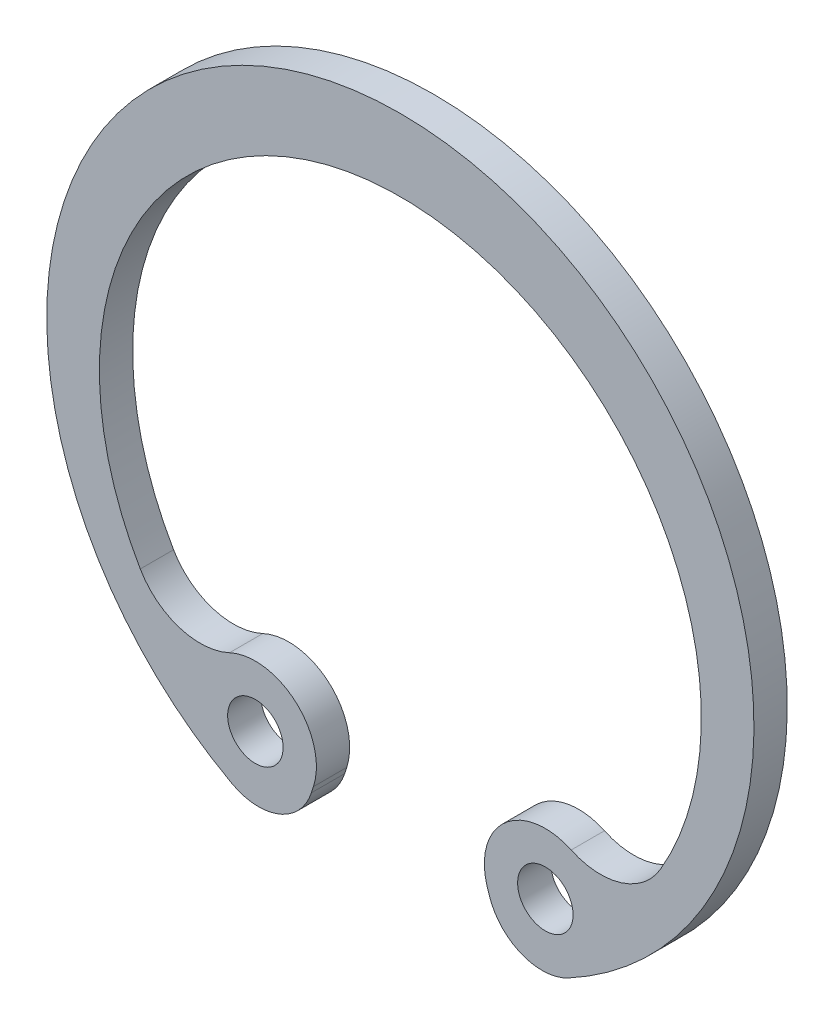
SolidWorks part; units mm, degrees
material "AISI 1020"
ref_plane "Спереди" through (0, 0, 0) normal (0, 0, 1) x (1, 0, 0)
ref_plane "Сверху" through (0, 0, 0) normal (0, 1, 0) x (1, 0, 0)
ref_plane "Справа" through (0, 0, 0) normal (1, 0, 0) x (0, 0, -1)
sketch "Эскиз1" plane through (0, 0, 0) normal (0, 0, 1) x (1, 0, 0)
  line L0 (0, -1000) -> (0, 49000) construction
  line L1 (0, 0) -> (5.7, -9.1144) construction
  line L2 (3.6355, -9.8745) -> (3.7195, -10.1028)
  line L3 (0, 10.35) -> (22.1, 10.35) construction
  arc A0 (6.6186, -11.1309) -> (0, 12.95) centre (0, 0) ccw
  circle A2 centre (5.7, -9.1144) radius 1
  arc A3 (6.5493, -7.085) -> (3.6355, -9.8745) centre (5.7, -9.1144) ccw
  arc A4 (6.5493, -7.085) -> (9.7116, -5.9714) centre (7.5144, -4.7788) ccw
  arc A5 (3.7195, -10.1028) -> (6.6186, -11.1309) centre (5.5964, -9.4119) ccw
  arc A6 (9.7116, -5.9714) -> (0, 10.35) centre (0, -0.7) ccw
  dimension "_d2" = 25.9
  dimension "_d4" = 2
  dimension "_r1" = 2.5
  dimension "_r2" = 2
  dimension "D1" = 11.05
  dimension "_e" = 0.7
  dimension "_a" = 4.4
  dimension "_l" = 7
  dimension "_d3" = 22.1
sketch "Эскиз2" plane through (0, 0, 0) normal (0, 0, 1) x (1, 0, 0)
  line L0 (0, -201000) -> (0, 249000) construction
  line L1 (-3.2086, -10.0704) -> (-3.1339, -9.8388)
  line L2 (3.6355, -9.8745) -> (3.7195, -10.1028) construction
  line L3 (0, 0) -> (6.6186, -11.1309) construction
  line L4 (0, 0) -> (-6.0632, -11.2161) construction
  line L5 (3.7195, -10.1028) -> (6.6186, -11.1309) construction
  line L6 (-6.0632, -11.2161) -> (-3.2086, -10.0704) construction
  line L7 (6.5493, -7.085) -> (3.6355, -9.8745) construction
  line L8 (-6.1593, -7.1707) -> (-3.1339, -9.8388) construction
  line L9 (0, 12.75) -> (0, 13.95) construction
  circle A0 centre (0, 0) radius 12.75 construction
  circle A1 centre (0, 0) radius 12 construction
  circle A2 centre (0, 0) radius 7.1 construction
  arc A3 (0, 12.75) -> (-6.0632, -11.2161) centre (0, 0) ccw
  arc A4 (0, 10.15) -> (-9.3782, -6.1639) centre (0, -0.7025) ccw
  arc A5 (-6.0632, -11.2161) -> (-3.2086, -10.0704) centre (-5.1121, -9.4567) ccw
  arc A6 (-3.1339, -9.8388) -> (-6.1593, -7.1707) centre (-5.2278, -9.1637) ccw
  arc A7 (3.7195, -10.1028) -> (6.6186, -11.1309) centre (5.5964, -9.4119) ccw construction
  arc A8 (6.5493, -7.085) -> (3.6355, -9.8745) centre (5.7, -9.1144) ccw construction
  arc A9 (-9.3782, -6.1639) -> (-6.1593, -7.1707) centre (-7.2178, -4.9058) ccw
  circle A10 centre (-5.2278, -9.1637) radius 1
  circle A11 centre (5.7, -9.1144) radius 1 construction
  arc A13 (6.5493, -7.085) -> (9.7116, -5.9714) centre (7.5144, -4.7788) ccw construction
  dimension "_D" = 24
  dimension "_d1" = 25.5
  dimension "_DD" = 14.2
  dimension "_b" = 2.6
  dimension "D1" = 149.264
  dimension "D2" = 12.95
  dimension "D3" = 151.605
  dimension "_s" = 1.2
sketch "Эскиз3" plane through (0, 0, 0) normal (0, 0, 1) x (1, 0, 0)
  line L0 (-3.2086, -10.0704) -> (-3.1339, -9.8388) construction
  line L1 (-3.2086, -10.0704) -> (-3.1339, -9.8388)
  line L2 (0, -1000) -> (0, 49000) construction
  line L3 (0, -1000.0733) -> (0, 48999.9267) construction
  line L4 (3.2086, -10.0704) -> (3.1339, -9.8388)
  arc A0 (0, 10.15) -> (-9.3782, -6.1639) centre (0, -0.7025) ccw construction
  arc A1 (-9.3782, -6.1639) -> (-6.1593, -7.1707) centre (-7.2178, -4.9058) ccw construction
  arc A2 (-3.1339, -9.8388) -> (-6.1593, -7.1707) centre (-5.2278, -9.1637) ccw construction
  arc A3 (-6.0632, -11.2161) -> (-3.2086, -10.0704) centre (-5.1121, -9.4567) ccw construction
  arc A4 (0, 12.75) -> (-6.0632, -11.2161) centre (0, 0) ccw construction
  arc A5 (9.3782, -6.1639) -> (-9.3782, -6.1639) centre (0, -0.7025) ccw
  arc A6 (-9.3782, -6.1639) -> (-6.1593, -7.1707) centre (-7.2178, -4.9058) ccw
  arc A7 (-3.1339, -9.8388) -> (-6.1593, -7.1707) centre (-5.2278, -9.1637) ccw
  arc A8 (-6.0632, -11.2161) -> (-3.2086, -10.0704) centre (-5.1121, -9.4567) ccw
  arc A9 (6.0632, -11.2161) -> (-6.0632, -11.2161) centre (0, 0) ccw
  circle A10 centre (-5.2278, -9.1637) radius 1 construction
  circle A11 centre (-5.2278, -9.1637) radius 1
  circle A12 centre (5.2278, -9.1637) radius 1
  arc A13 (9.3782, -6.1639) -> (6.1593, -7.1707) centre (7.2178, -4.9058) cw
  arc A14 (3.1339, -9.8388) -> (6.1593, -7.1707) centre (5.2278, -9.1637) cw
  arc A15 (6.0632, -11.2161) -> (3.2086, -10.0704) centre (5.1121, -9.4567) cw
extrude "Бобышка-Вытянуть1" add sketch "Эскиз3" along normal blind 1.2
equation "\"D1@Эскиз1\"=\"_d3@Эскиз1\"/2"
equation "\"D3@Эскиз2\"=(\"D2@Эскиз2\"*2*\"D1@Эскиз2\"/360)/(\"_d1@Эскиз2\"/360)"
equation "\"D1@Бобышка-Вытянуть1\"= \"_s@Эскиз2\""
